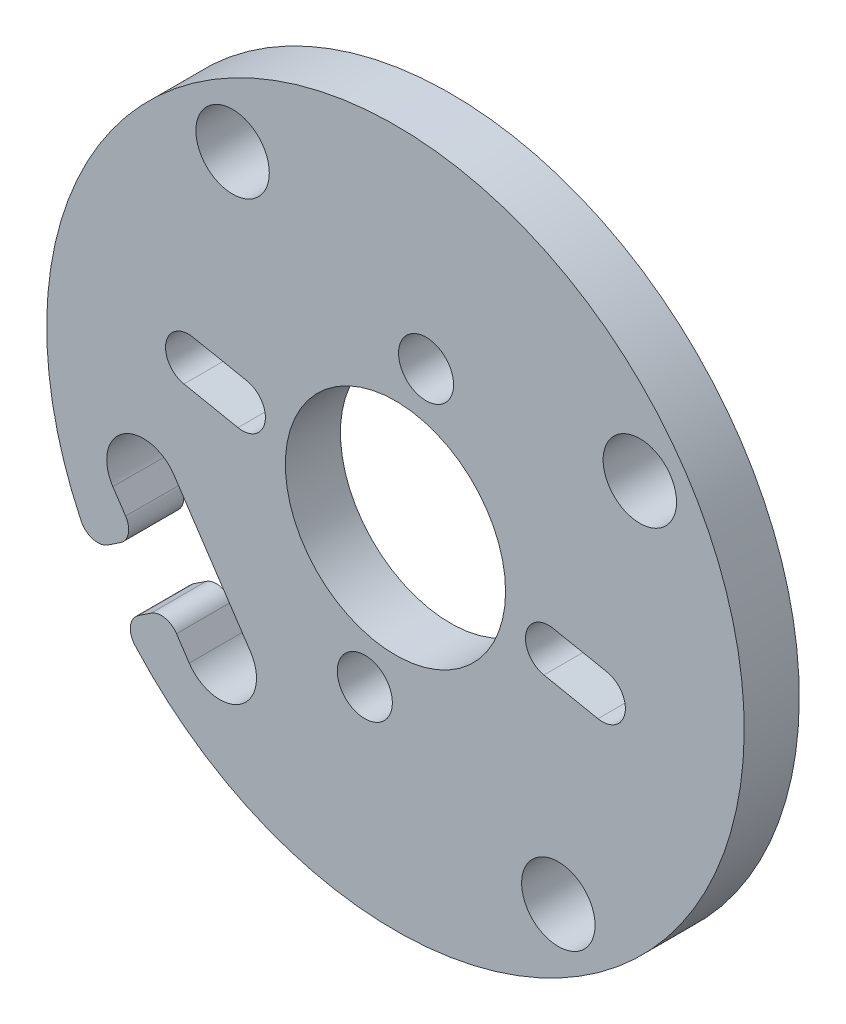
SolidWorks part; units mm, degrees
ref_plane "Front Plane" through (0, 0, 0) normal (0, 0, 1) x (1, 0, 0)
ref_plane "Top Plane" through (0, 0, 0) normal (0, 1, 0) x (1, 0, 0)
ref_plane "Right Plane" through (0, 0, 0) normal (1, 0, 0) x (0, 0, -1)
sketch "Sketch1" plane through (0, 0, 0) normal (0, 0, 1) x (1, 0, 0)
  line L0 (-8.8736, 13.3139) -> (8.8736, -13.3139) construction
  line L1 (1.668, 8.3347) -> (0, 0) construction
  line L2 (0, 0) -> (-11.2764, 2.2567) construction
  line L3 (-11.2764, 2.2567) -> (-8.3347, 1.668) construction
  line L4 (-11.0311, 3.4824) -> (-8.0894, 2.8937)
  line L5 (-11.5217, 1.031) -> (-8.58, 0.4423)
  line L6 (11.2762, -2.2577) -> (8.3346, -1.6687) construction
  line L7 (11.0308, -3.4834) -> (8.0892, -2.8944)
  line L8 (11.5216, -1.032) -> (8.58, -0.4431)
  line L9 (-13.7294, -4.6439) -> (-9.5699, -10.8848) construction
  line L10 (-12.0652, -3.5347) -> (-7.9057, -9.7756)
  line L11 (-15.3936, -5.7531) -> (-14.7004, -6.7933)
  line L12 (-11.6497, -7.7644) -> (0, 0) construction
  line L13 (-14.9779, -8.18) -> (-15.6649, -8.6378)
  line L14 (-11.9274, -10.9539) -> (-11.2342, -11.994)
  line L15 (-14.0011, -11.1342) -> (-13.3141, -10.6763)
  circle A1 centre (-8.8736, 13.3139) radius 2
  circle A2 centre (13.3139, 8.8736) radius 2
  circle A3 centre (8.8736, -13.3139) radius 2
  circle A4 centre (0, 0) radius 6
  circle A5 centre (-13.3139, -8.8736) radius 2 [skipped]
  circle A6 centre (1.668, 8.3347) radius 1.5
  circle A7 centre (-1.668, -8.3347) radius 1.5
  arc A8 (-11.0311, 3.4824) -> (-11.5217, 1.031) centre (-11.2764, 2.2567) ccw
  arc A9 (-8.58, 0.4423) -> (-8.0894, 2.8937) centre (-8.3347, 1.668) ccw
  arc A10 (11.0308, -3.4834) -> (11.5216, -1.032) centre (11.2762, -2.2577) ccw
  arc A11 (8.58, -0.4431) -> (8.0892, -2.8944) centre (8.3346, -1.6687) ccw
  arc A12 (-12.0652, -3.5347) -> (-15.3936, -5.7531) centre (-13.7294, -4.6439) ccw
  arc A13 (-11.2342, -11.994) -> (-7.9057, -9.7756) centre (-9.5699, -10.8848) ccw
  arc A14 (-11.9274, -10.9539) -> (-13.3141, -10.6763) centre (-12.7595, -11.5085) ccw
  arc A15 (-14.9779, -8.18) -> (-14.7004, -6.7933) centre (-15.5325, -7.3479) ccw
  arc A16 (-14.1935, -12.6311) -> (-14.0011, -11.1342) centre (-13.4465, -11.9663) cw
  arc A17 (-17.1205, -8.2394) -> (-15.6649, -8.6378) centre (-16.2195, -7.8057) ccw
  arc A19 (-14.1935, -12.6311) -> (-17.1205, -8.2394) centre (0, 0) ccw
  point P14 (0, 0)
  point P20 (0, 0)
  point P21 (-9.8056, 1.9624)
  point P28 (-11.6497, -7.7644)
  point P31 (9.8054, -1.9632)
  point P36 (0, 0)
  dimension "D4" = 12
  dimension "D5" = 3
  dimension "D6" = 4
  dimension "D20" = 1
  dimension "D22" = 1
  dimension "D2" = 16
  dimension "D8" = 8.5
  dimension "D9" = 45
  dimension "D10" = 45
  dimension "D11" = 3
  dimension "D12" = 2.5
  dimension "D14" = 10
  dimension "D15" = 10
  dimension "D16" = 7.5
  dimension "D17" = 4
  dimension "D18" = 14
  dimension "D19" = 3
  dimension "D21" = 1.5
  dimension "D3" = 4
  dimension "D7" = 2
  dimension "D13" = 2
extrude "Boss-Extrude1" add sketch "Sketch1" along normal blind 3
equation "\"D8@Sketch1\"=17/2"
equation "\"D14@Sketch1\"=20/2"
